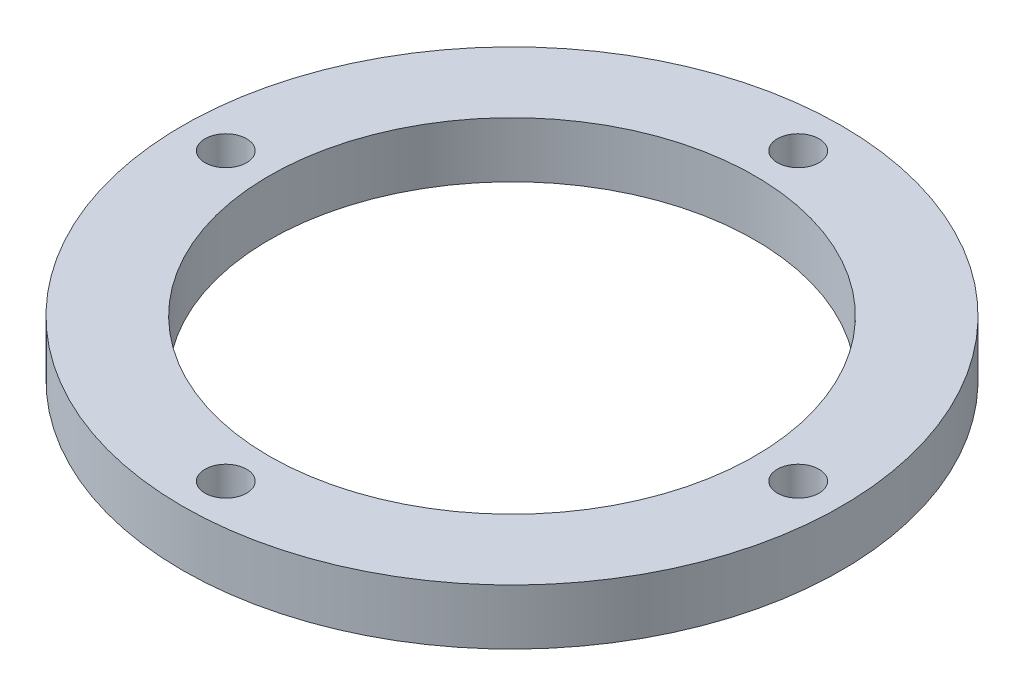
SolidWorks part; units mm, degrees
ref_plane "前视基准面" through (0, 0, 0) normal (0, 0, 1) x (1, 0, 0)
ref_plane "上视基准面" through (0, 0, 0) normal (0, 1, 0) x (1, 0, 0)
ref_plane "右视基准面" through (0, 0, 0) normal (1, 0, 0) x (0, 0, -1)
other "Configuration Table"
sketch "草图1" plane through (0, 0, 0) normal (0, 1, 0) x (1, 0, 0)
  circle A0 centre (0, 0) radius 47.5
  circle A1 centre (0, 0) radius 35
  circle A2 centre (41.25, 0) radius 3
  circle A3 centre (0, -41.25) radius 3
  circle A4 centre (-41.25, 0) radius 3
  circle A5 centre (0, 41.25) radius 3
  point P17 (0, 0)
  dimension "D1" = 95
  dimension "D2" = 4
extrude "凸台-拉伸1" add sketch "草图1" along normal blind 8
